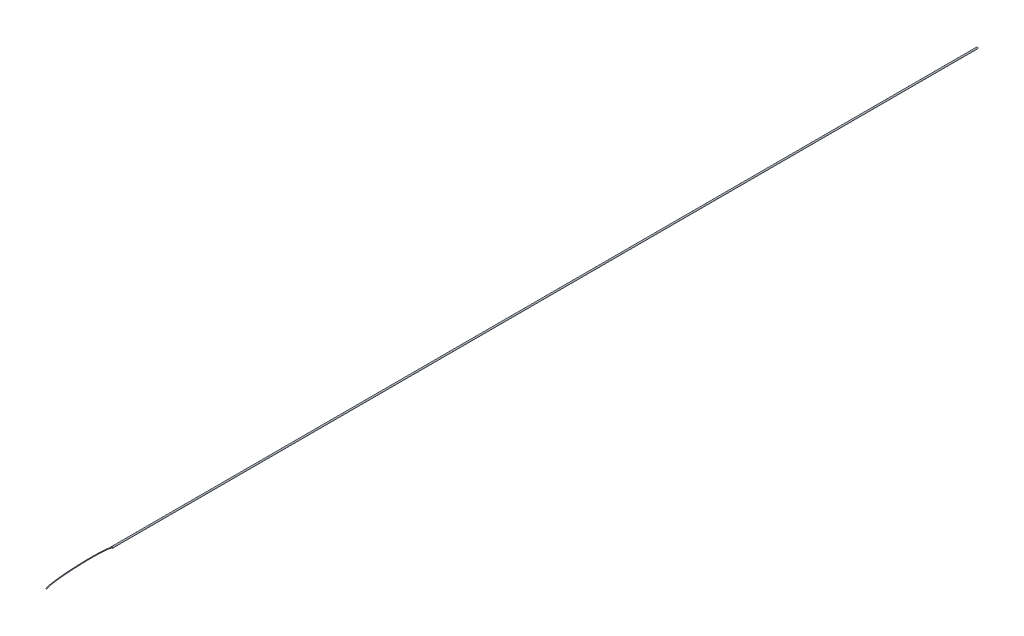
SolidWorks part; units mm, degrees
ref_plane "Front Plane" through (0, 0, 0) normal (0, 0, 1) x (1, 0, 0)
ref_plane "Top Plane" through (0, 0, 0) normal (0, 1, 0) x (1, 0, 0)
ref_plane "Right Plane" through (0, 0, 0) normal (1, 0, 0) x (0, 0, -1)
sketch "Sketch1" plane through (0, 0, 0) normal (0, 0, 1) x (1, 0, 0)
  circle A0 centre (0, 0) radius 1.143
  dimension "D1" = 2.286
sketch "Sketch3" plane through (0, 0, 0) normal (0, 1, 0) x (1, 0, 0)
  line L0 (0, 0) -> (0, -1389)
  dimension "D1" = 1389
sweep "Sweep1" add profiles "Sketch1" path "Sketch3"
sketch "Sketch4" plane through (0, 0, 1389) normal (0, 0, 1) x (1, 0, 0)
  circle A0 centre (0, 0) radius 0.5
  dimension "D1" = 1
sketch3d "3DSketch1"
  line L0 (0, 0, 1389) -> (0, 0, 0) construction
  spline S0 degree 3 poles (0, 0, 1389) (-1.5686, 3.926, 1405.9934) (17.5292, 18.6271, 1506.6968) (18.844, 13.9223, 1513) knots 0 0 0 0 1 1 1 1
sweep "Sweep2" add profiles "Sketch4" path "3DSketch1"
